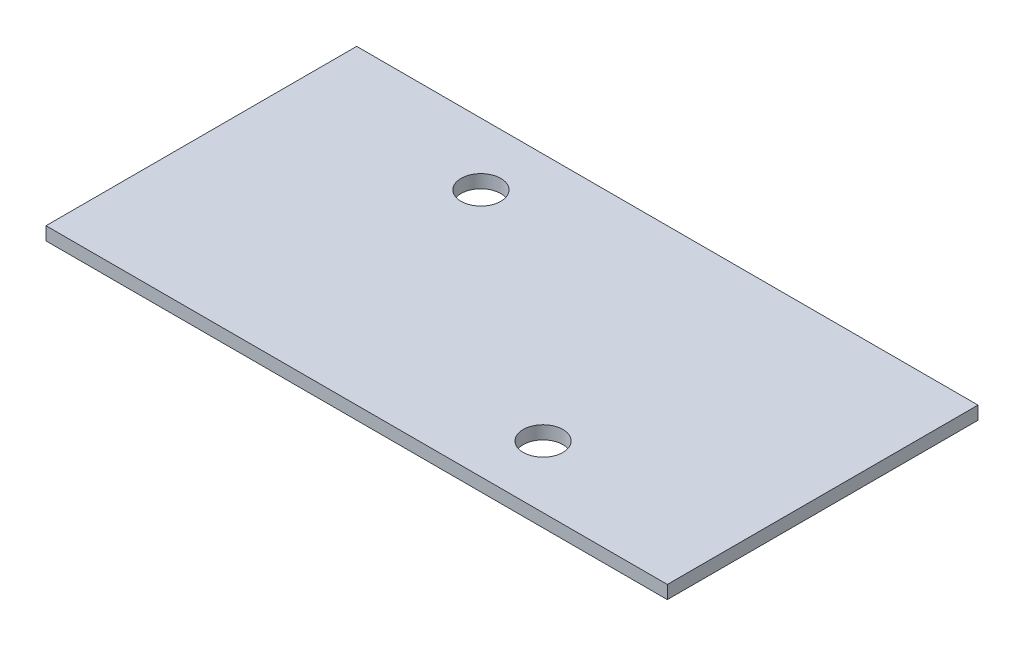
SolidWorks part; units mm, degrees
ref_plane "Front Plane" through (0, 0, 0) normal (0, 0, 1) x (1, 0, 0)
ref_plane "Top Plane" through (0, 0, 0) normal (0, 1, 0) x (1, 0, 0)
ref_plane "Right Plane" through (0, 0, 0) normal (1, 0, 0) x (0, 0, -1)
sketch "Sketch1" plane through (0, 0, 0) normal (0, 1, 0) x (1, 0, 0)
  line L1 (-25, 12.5) -> (25, 12.5)
  line L2 (-25, 12.5) -> (-25, -12.5)
  line L3 (-25, -12.5) -> (25, -12.5)
  line L4 (25, 12.5) -> (25, -12.5)
  line L5 (-25, 12.5) -> (25, -12.5) construction
  line L6 (-25, -12.5) -> (25, 12.5) construction
  point P0 (0, 0)
  dimension "D1" = 50
  dimension "D2" = 25
extrude "Boss-Extrude1" add sketch "Sketch1" along normal blind 1.06
sketch "Sketch2" plane through (0, 1.06, 0) normal (0, 1, 0) x (1, 0, 0)
  line L0 (0, 0) -> (0, 50000) construction
  line L1 (0, 0) -> (50000, 0) construction
  line L2 (10, 5.6757) -> (10, -49994.3243) construction
  line L3 (-10, 4.7845) -> (-10, -49995.2155) construction
  line L4 (-5.5576, 7.5) -> (49994.4424, 7.5) construction
  line L5 (28.2616, -7.5) -> (-49971.7384, -7.5) construction
  circle A1 centre (-10, 7.5) radius 1.6
  circle A3 centre (10, -7.5) radius 1.6
  dimension "D3" = 3.2
  dimension "D1" = 20
  dimension "D2" = 15
  dimension "D4" = 7.5
  dimension "D5" = 10
extrude "Cut-Extrude1" cut sketch "Sketch2" against normal through all
